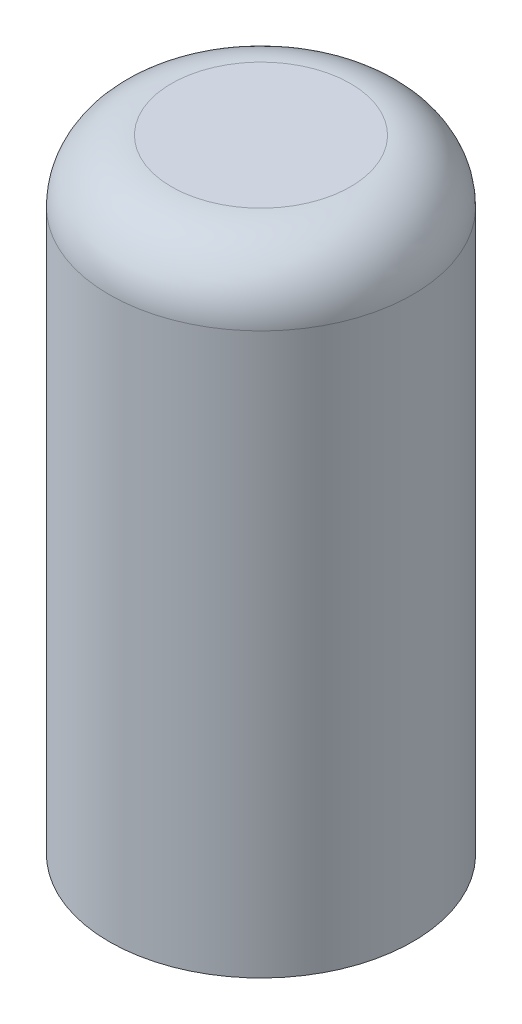
SolidWorks part; units mm, degrees
material "Ti-6Al-2Sn-2Zr-2Mo-2Cr-0.25Si (SS)"
ref_plane "Front Plane" through (0, 0, 0) normal (0, 0, 1) x (1, 0, 0)
ref_plane "Top Plane" through (0, 0, 0) normal (0, 1, 0) x (1, 0, 0)
ref_plane "Right Plane" through (0, 0, 0) normal (1, 0, 0) x (0, 0, -1)
sketch "Sketch1" plane through (0, 0, 0) normal (0, 1, 0) x (1, 0, 0)
  circle A0 centre (0, 0) radius 97.5
  dimension "D1" = 195
extrude "Boss-Extrude1" add sketch "Sketch1" along normal blind 650
sketch "Sketch2" plane through (0, 0, 0) normal (0, -1, 0) x (1, 0, 0)
  circle A0 centre (0, 0) radius 67.5
  circle A1 centre (0, 0) radius 97.5 construction
  circle A2 centre (0, 0) radius 97.5
  dimension "D1" = 30
  dimension "D2" = 195
extrude "Cut-Extrude4" cut sketch "Sketch2" against normal blind 250
sketch "Sketch4" plane through (0, 0, 0) normal (0, 0, 1) x (1, 0, 0)
  line L0 (0, 0) -> (0, 900) construction
  line L1 (97.5, 650) -> (-97.5, 650) construction
  circle A0 centre (0, 450) radius 67.5
  dimension "D1" = 135
  dimension "D2" = 200
extrude "Cut-Extrude3" cut sketch "Sketch4" against normal through all
fillet "Fillet1" radius 40 1 edges at (0, 650, 97.5)
sketch "Sketch5" plane through (0, 0, 0) normal (0, -1, 0) x (1, 0, 0)
  circle A0 centre (0, 0) radius 67.5
extrude "Cut-Extrude5" cut sketch "Sketch5" against normal blind 350
